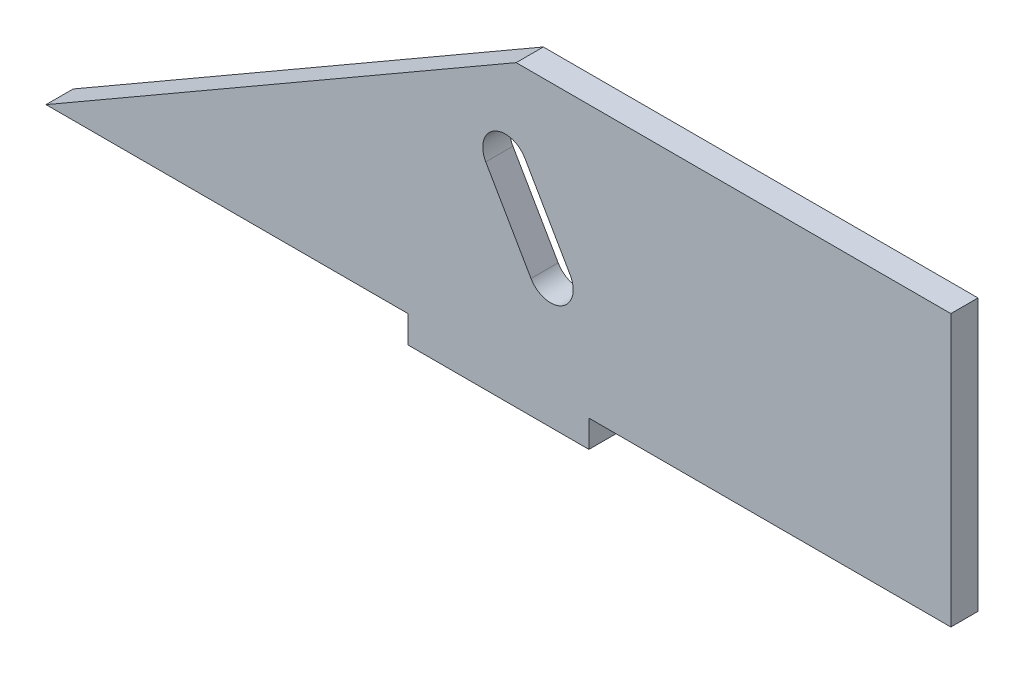
SolidWorks part; units mm, degrees
ref_plane "Front Plane" through (0, 0, 0) normal (0, 0, 1) x (1, 0, 0)
ref_plane "Top Plane" through (0, 0, 0) normal (0, 1, 0) x (1, 0, 0)
ref_plane "Right Plane" through (0, 0, 0) normal (1, 0, 0) x (0, 0, -1)
sketch "Sketch1" plane through (0, 0, 0) normal (0, 0, 1) x (1, 0, 0)
  line L0 (-10, -13) -> (-10, -16)
  line L1 (50, -13) -> (10, -13)
  line L2 (50, -13) -> (50, 17)
  line L3 (50, 17) -> (-50, 17)
  line L4 (-50, -13) -> (-50, 17)
  line L5 (50, -13) -> (-50, 17) construction
  line L6 (50, 17) -> (-50, -13) construction
  line L7 (-10, -16) -> (10, -16)
  line L8 (10, -16) -> (10, -13)
  line L9 (-10, -13) -> (-50, -13)
  point P0 (0, 2)
  point P9 (10, -14.5)
  dimension "D1" = 40
  dimension "D2" = 30
  dimension "D3" = 3
  dimension "D4" = 20
  dimension "D5" = 40
extrude "Boss-Extrude1" add sketch "Sketch1" along normal blind 3
sketch "Sketch2" plane through (0, 0, 3) normal (0, 0, 1) x (1, 0, 0)
  line L0 (-50, -13) -> (1.9615, 17)
  line L1 (50, 17) -> (-50, 17) construction
  line L2 (-50, 17) -> (-50, -13) construction
  line L3 (1.9615, 17) -> (-50, 17)
  line L4 (-50, 17) -> (-50, -13)
  dimension "D1" = 60
extrude "Cut-Extrude1" cut sketch "Sketch2" against normal blind 4
sketch "Sketch4" plane through (0, 0, 3) normal (0, 0, 1) x (1, 0, 0)
  line L0 (1.9615, 17) -> (18.577, -11.7788) construction
  line L1 (-50, -13) -> (1.9615, 17) construction
  line L2 (7.9304, -0.3385) -> (2.9304, 8.3218)
  line L3 (3.6003, -2.8385) -> (-1.3997, 5.8218)
  arc A0 (2.9304, 8.3218) -> (-1.3997, 5.8218) centre (0.7654, 7.0718) ccw
  arc A1 (3.6003, -2.8385) -> (7.9304, -0.3385) centre (5.7654, -1.5885) ccw
  dimension "D5" = 5
  dimension "D6" = 5
  dimension "D1" = 8
  dimension "D2" = 6
  dimension "D3" = 6
  dimension "D4" = 10
extrude "Cut-Extrude2" cut sketch "Sketch4" against normal blind 4
